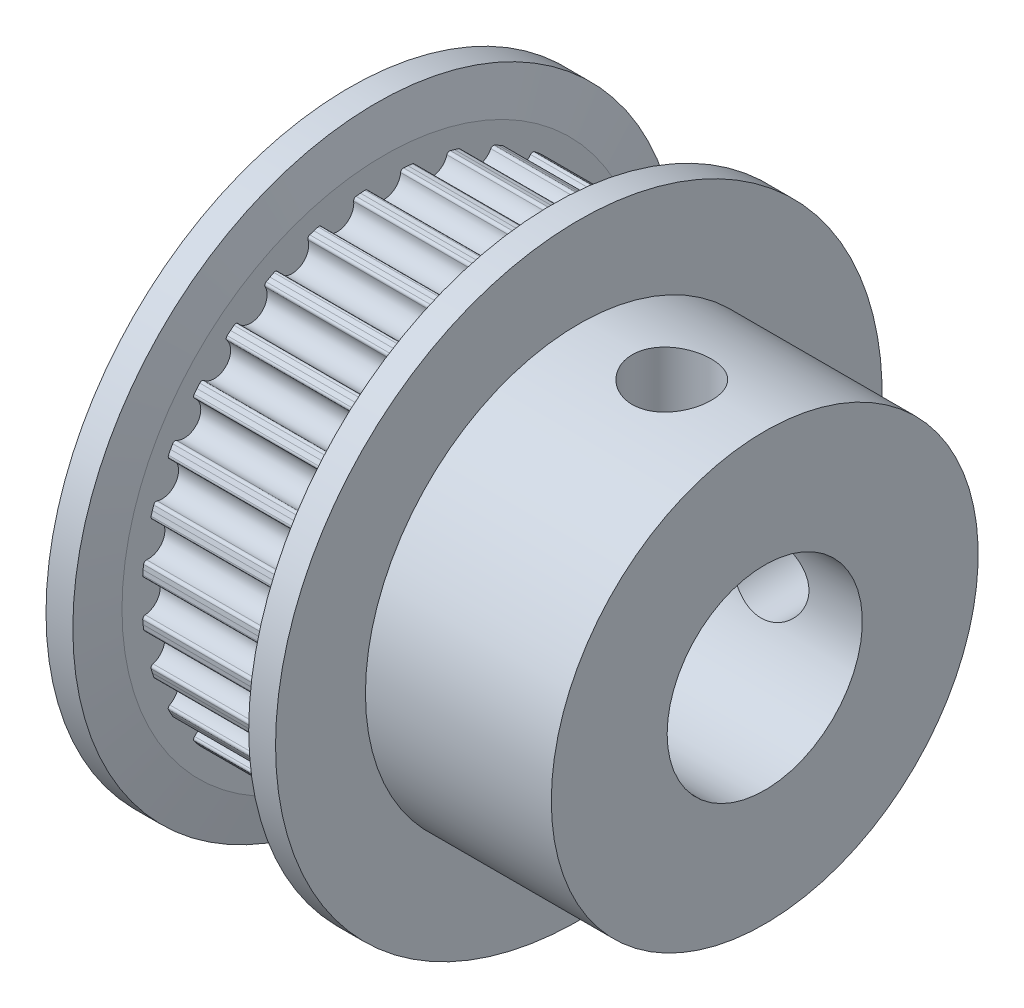
SolidWorks part; units mm, degrees
ref_plane "Front Plane" through (0, 0, 0) normal (0, 0, 1) x (1, 0, 0)
ref_plane "Top Plane" through (0, 0, 0) normal (0, 1, 0) x (1, 0, 0)
ref_plane "Right Plane" through (0, 0, 0) normal (1, 0, 0) x (0, 0, -1)
ref_plane "Plane1" through (0, 0, 0) normal (0, 0, 1) x (1, 0, 0)
sketch "Sketch1" plane through (0, 0, 0) normal (0, 0, 1) x (1, 0, 0)
  line L0 (0, 0) -> (0, 8.75)
  line L1 (0, 8.75) -> (1.43, 8.75)
  line L2 (1.43, 8.75) -> (1.43, 10.0881)
  line L3 (1.43, 10.0881) -> (7.98, 10.0881)
  line L4 (7.98, 10.0881) -> (7.98, 8.75)
  line L5 (7.98, 8.75) -> (17.03, 8.75)
  line L6 (17.03, 8.75) -> (17.03, 0)
  line L7 (17.03, 0) -> (0, 0)
  line L8 (17.03, 0) -> (0, 0) construction
  dimension "D1" = 6.55
  dimension "D2" = 8.75
  dimension "D3" = 1.43
  dimension "D4" = 9.05
  dimension "D5" = 10.0881
revolve "Revolve1" add sketch "Sketch1" angle 360 about L8
sketch "Sketch2" plane through (1.43, 0, 0) normal (1, 0, 0) x (0, 0, -1)
  line L0 (-1.0344, 9.88) -> (-1.0578, 10.1299)
  line L1 (-0.793, 9.8993) -> (-1.0344, 9.88)
  line L2 (0.793, 9.8993) -> (1.0344, 9.88)
  line L3 (1.0344, 9.88) -> (1.0578, 10.1299)
  line L4 (0, 10.185) -> (0, 0) construction
  arc A0 (-0.6724, 9.7974) -> (-0.793, 9.8993) centre (-0.784, 9.7876) ccw
  arc A1 (-0.6724, 9.7974) -> (0.6724, 9.7974) centre (0, 9.856) ccw
  arc A2 (0.6724, 9.7974) -> (0.793, 9.8993) centre (0.784, 9.7876) cw
  arc A3 (1.0578, 10.1299) -> (-1.0578, 10.1299) centre (0, 0) ccw
  dimension "D2" = 0.675
  dimension "D1" = 9.856
  dimension "D3" = 9.931
extrude "Cut-Extrude1" cut sketch "Sketch2" against normal up to surface
ref_axis "Axis1" through (17.03, 0, 0) along (-1, 0, 0)
pattern_circular "CirPattern1" count 32 over 360 about axis through (0, 0, 0) along (1, 0, 0) of "Cut-Extrude1"
sketch "Sketch34" plane through (0, 0, 0) normal (0, 0, 1) x (1, 0, 0)
  line L0 (7.98, 8.75) -> (7.98, 10.75)
  line L1 (7.98, 10.75) -> (8.31, 12.435)
  line L2 (8.31, 12.435) -> (9.41, 12.435)
  line L3 (9.41, 12.435) -> (9.41, 8.75)
  line L4 (17.03, 8.75) -> (7.98, 8.75) construction
  line L5 (9.41, 8.75) -> (7.98, 8.75)
  line L6 (17.03, 0) -> (7.98, 0) construction
  line L7 (1.43, 8.75) -> (1.43, 10.75)
  line L8 (1.43, 10.75) -> (1.1, 12.435)
  line L9 (1.1, 12.435) -> (0, 12.435)
  line L10 (0, 12.435) -> (0, 8.76)
  line L11 (0.01, 8.75) -> (1.43, 8.75)
  line L12 (0, 8.76) -> (0.01, 8.75)
  point P16 (0, 8.75)
  dimension "D1" = 1.43
  dimension "D2" = 12.435
  dimension "D3" = 1.1
  dimension "D4" = 10.75
revolve "Revolve2" add sketch "Sketch34" angle 360 about L6
sketch "Sketch39" plane through (0, 0, 0) normal (-1, 0, 0) x (0, 0, 1)
  circle A0 centre (0, 0) radius 4.001
  dimension "D1" = 8.002
extrude "Cut-Extrude2" cut sketch "Sketch39" against normal up to surface (17.03 mm away) up to face at (17.03, 0, 8.75)
ref_plane "Plane39" through (13.22, 0, 0) normal (1, 0, 0) x (0, 0, -1)
sketch "Sketch37" plane through (13.22, 0, 0) normal (1, 0, 0) x (0, 0, -1)
  line L0 (0, 9.93) -> (1.621, 9.93)
  line L1 (1.621, 9.93) -> (1.621, 0)
  line L2 (1.621, 0) -> (0, 0)
  line L3 (0, 0) -> (0, 9.93)
  line L4 (0, 0) -> (0, 9.93) construction
revolve "Cut-Revolve2" cut sketch "Sketch37" angle 360 about L4
pattern_circular "CirPattern2" count 2 over 90 about axis through (17.03, 0, 0) along (-1, 0, 0) of "Cut-Revolve2"
ref_plane "Plane40" through (4.705, 0, 0) normal (-1, 0, 0) x (0, 0, 1)
sketch "Sketch40" plane through (4.705, 0, 0) normal (-1, 0, 0) x (0, 0, 1)
  circle A0 centre (0, 0) radius 9.9327
